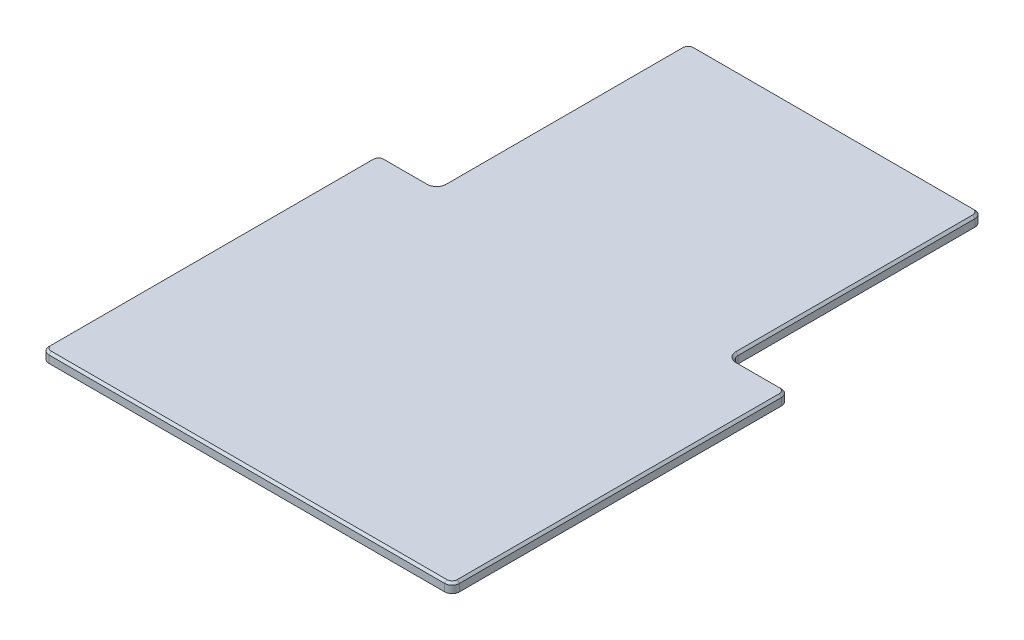
SolidWorks part; units mm, degrees
ref_plane "Front Plane" through (0, 0, 0) normal (0, 0, 1) x (1, 0, 0)
ref_plane "Top Plane" through (0, 0, 0) normal (0, 1, 0) x (1, 0, 0)
ref_plane "Right Plane" through (0, 0, 0) normal (1, 0, 0) x (0, 0, -1)
sketch "Sketch1" plane through (0, 0, 0) normal (0, 1, 0) x (1, 0, 0)
  line L1 (10, 0) -> (548, 0)
  line L2 (0, 10) -> (0, 448)
  line L3 (10, 458) -> (69, 458)
  line L4 (558, 10) -> (558, 448)
  line L6 (79, 468) -> (79, 790)
  line L7 (89, 800) -> (469, 800)
  line L8 (479, 468) -> (479, 790)
  line L9 (489, 458) -> (548, 458)
  arc A0 (469, 800) -> (479, 790) centre (469, 790) cw
  arc A1 (79, 790) -> (89, 800) centre (89, 790) cw
  arc A2 (548, 458) -> (558, 448) centre (548, 448) cw
  arc A3 (548, 0) -> (558, 10) centre (548, 10) ccw
  arc A4 (10, 0) -> (0, 10) centre (10, 10) cw
  arc A5 (69, 458) -> (79, 468) centre (69, 468) ccw
  arc A6 (479, 468) -> (489, 458) centre (489, 468) ccw
  arc A7 (0, 448) -> (10, 458) centre (10, 448) cw
  point P17 (558, 0)
  point P20 (0, 0)
  point P29 (0, 458)
  dimension "D6" = 10
  dimension "D7" = 10
  dimension "D8" = 10
  dimension "D1" = 558
  dimension "D2" = 458
  dimension "D3" = 342
  dimension "D4" = 400
  dimension "D5" = 79
extrude "Boss-Extrude2" add sketch "Sketch1" along normal blind 13
chamfer "Chamfer2" distance 3 angle 45 16 edges at (479, 13, -629) (518.5, 13, -458) (558, 13, -229) (279, 13, 0) (0, 13, -229) (79, 13, -629) (555.0711, 13, -2.9289) (2.9289, 13, -2.9289) (555.0711, 13, -455.0711) (2.9289, 13, -455.0711) (39.5, 13, -458) (481.9289, 13, -460.9289) (76.0711, 13, -460.9289) (476.0711, 13, -797.0711) (81.9289, 13, -797.0711) (279, 13, -800)
